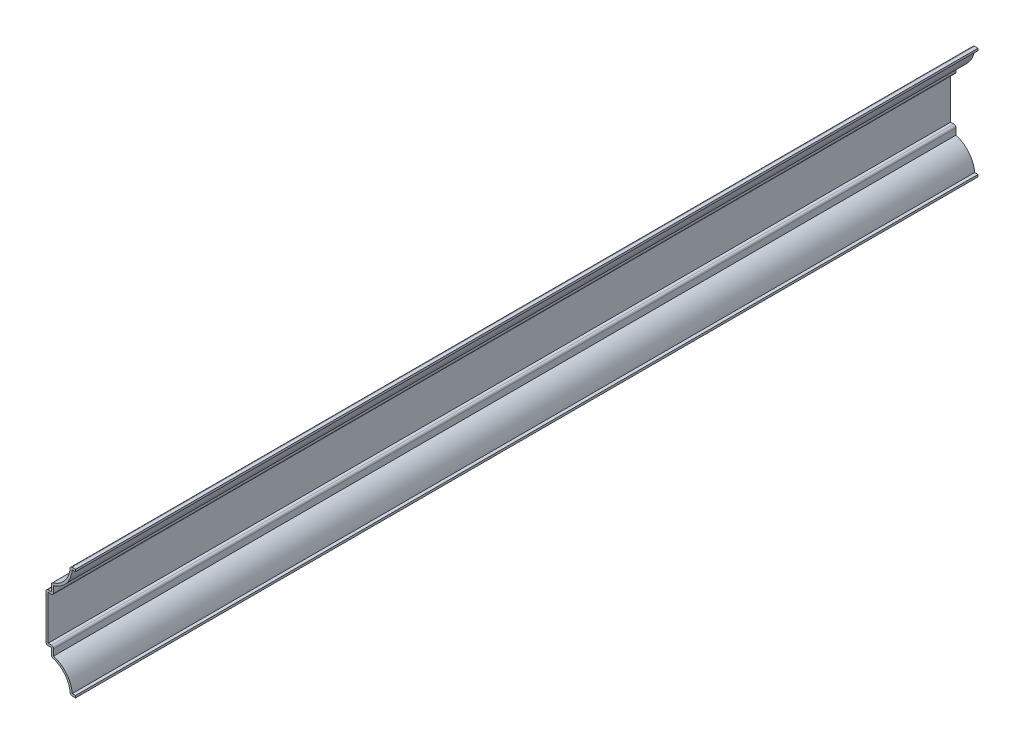
SolidWorks part; units mm, degrees
ref_plane "Front Plane" through (0, 0, 0) normal (0, 0, 1) x (1, 0, 0)
ref_plane "Top Plane" through (0, 0, 0) normal (0, 1, 0) x (1, 0, 0)
ref_plane "Right Plane" through (0, 0, 0) normal (1, 0, 0) x (0, 0, -1)
sketch "Sketch1" plane through (0, 0, 0) normal (0, 0, 1) x (1, 0, 0)
  line L0 (-17.4625, 0) -> (0, 0) construction
  line L1 (0, 0) -> (0, 32.9406) construction
  line L2 (0, 32.9406) -> (-17.4625, 32.9406) construction
  line L3 (0, 0) -> (-3.175, 0)
  line L4 (-14.2875, 13.8906) -> (-14.2875, 18.6531)
  line L5 (-14.2875, 18.6531) -> (-17.4625, 18.6531)
  line L6 (-17.4625, 18.6531) -> (-17.4625, 47.2281)
  line L7 (-14.2875, 47.2281) -> (-17.4625, 47.2281)
  line L8 (-14.2875, 51.9906) -> (-14.2875, 47.2281)
  line L9 (0, 65.8813) -> (-3.175, 65.8813)
  arc A0 (-3.175, 0) -> (-14.2875, 13.8906) centre (-17.4129, 0) ccw
  arc A1 (-3.175, 65.8813) -> (-14.2875, 51.9906) centre (-17.4129, 65.8813) cw
  point P5 (-19.6392, -1.781)
  point P8 (-16.39, 32.9406)
  dimension "D1" = 65.8813
  dimension "D2" = 17.4625
  dimension "D3" = 3.175
  dimension "D4" = 11.1125
  dimension "D5" = 13.8906
  dimension "D6" = 4.7625
extrude "Extrude-Thin1" add sketch "Sketch1" against normal blind 533.4 thin
fillet "Fillet1" radius 1.27 8 edges at (-3.175, 0, -266.7) (-14.2875, 13.8906, -266.7) (-17.4625, 18.6531, -266.7) (-13.0175, 19.9231, -266.7) (-17.4625, 47.2281, -266.7) (-13.0175, 45.9581, -266.7) (-14.2875, 51.9906, -266.7) (-3.175, 65.8813, -266.7)
